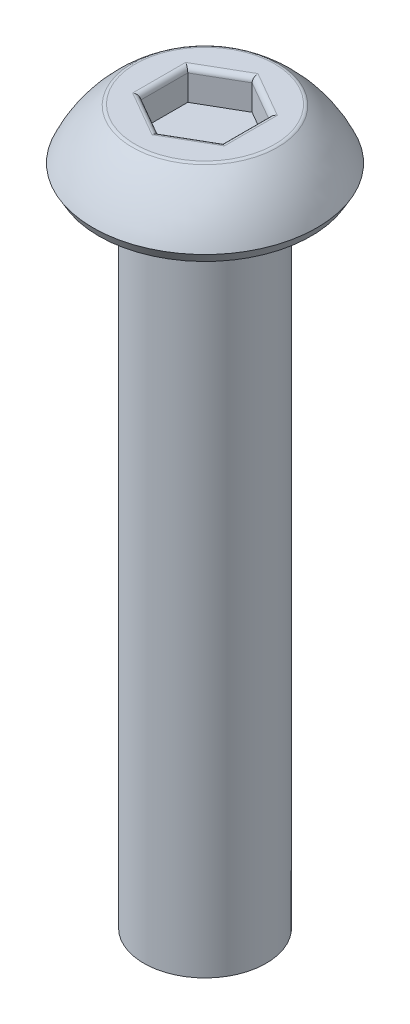
SolidWorks part; units mm, degrees
ref_plane "Front Plane" through (0, 0, 0) normal (0, 0, 1) x (1, 0, 0)
ref_plane "Top Plane" through (0, 0, 0) normal (0, 1, 0) x (1, 0, 0)
ref_plane "Right Plane" through (0, 0, 0) normal (1, 0, 0) x (0, 0, -1)
sketch "Sketch1" plane through (0, 0, 0) normal (1, 0, 0) x (0, 0, -1)
  line L0 (0, 0) -> (0, 1.5) construction
  line L1 (0, 1.5) -> (-1.75, 1.5)
  line L3 (-2.75, 0.25) -> (-2.6057, 0)
  line L4 (-2.6057, 0) -> (-1.5, 0)
  line L5 (-1.5, 0) -> (-1.5, -16)
  line L6 (-1.5, -16) -> (0, -16)
  line L7 (0, -16) -> (0, 1.5)
  line L8 (0, 0) -> (-1.5, 0) construction
  arc A0 (-1.75, 1.5) -> (-2.75, 0.25) centre (0.0077, -0.9312) ccw
  dimension "D5" = 3
  dimension "D1" = 1.5
  dimension "D2" = 2.75
  dimension "D3" = 1.75
  dimension "D4" = 0.25
  dimension "D6" = 60
  dimension "D7" = 1.5
  dimension "D8" = 16
revolve "Revolve1" add sketch "Sketch1" angle 360 about L7
sketch "Sketch2" plane through (0, 1.5, 0) normal (0, 1, 0) x (1, 0, 0)
  line L1 (0, 1.1547) -> (-1, 0.5774)
  line L2 (-1, 0.5774) -> (-1, -0.5774)
  line L3 (-1, -0.5774) -> (0, -1.1547)
  line L4 (0, -1.1547) -> (1, -0.5774)
  line L5 (1, -0.5774) -> (1, 0.5774)
  line L6 (1, 0.5774) -> (0, 1.1547)
  circle A0 centre (0, 0) radius 1 construction
  dimension "D1" = 2
extrude "Cut-Extrude1" cut sketch "Sketch2" against normal blind 0.75
fillet "Fillet1" radius 0.125 7 edges at (0, 1.5, -1.75) (-0.5, 1.5, 0.866) (0.5, 1.5, 0.866) (1, 1.5, 0) (0.5, 1.5, -0.866) (-0.5, 1.5, -0.866) (-1, 1.5, 0)
